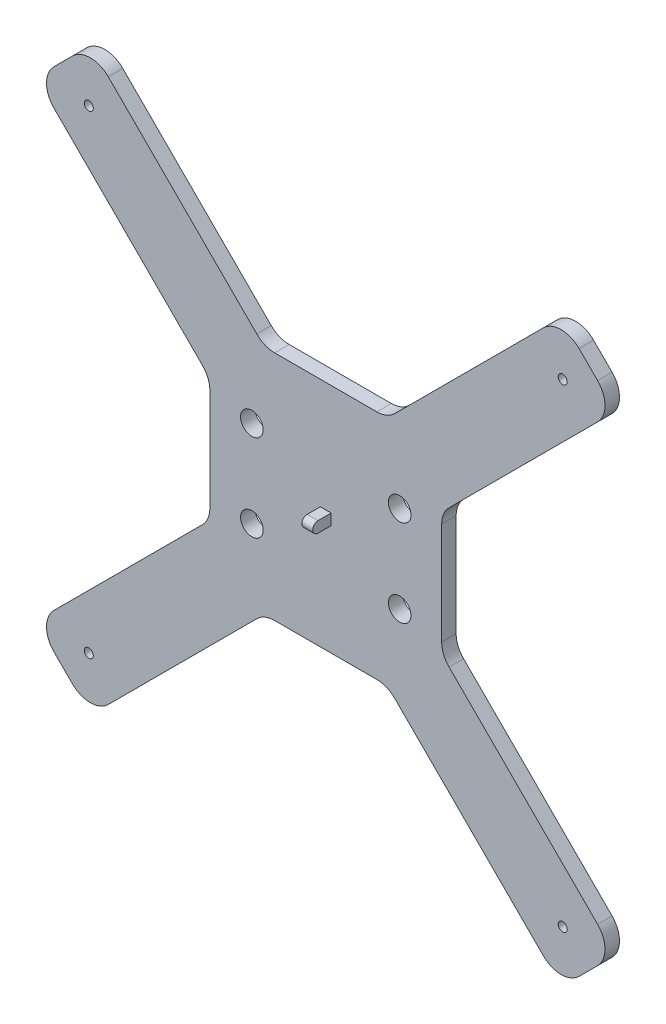
SolidWorks part; units mm, degrees
ref_plane "Front Plane" through (0, 0, 0) normal (0, 0, 1) x (1, 0, 0)
ref_plane "Top Plane" through (0, 0, 0) normal (0, 1, 0) x (1, 0, 0)
ref_plane "Right Plane" through (0, 0, 0) normal (1, 0, 0) x (0, 0, -1)
sketch "Sketch1" plane through (0, 0, 0) normal (0, 0, 1) x (1, 0, 0)
  line L0 (0, 184.15) -> (60.96, 123.19)
  line L5 (19.05, 203.2) -> (80.01, 142.24)
  line L6 (0, 19.05) -> (60.96, 80.01)
  line L7 (19.05, 0) -> (80.01, 60.96)
  line L8 (0, 184.15) -> (19.05, 203.2)
  line L9 (184.15, 203.2) -> (203.2, 184.15)
  line L10 (203.2, 19.05) -> (184.15, 0)
  line L11 (0, 19.05) -> (19.05, 0)
  line L12 (80.01, 142.24) -> (123.19, 142.24)
  line L13 (80.01, 60.96) -> (123.19, 60.96)
  line L14 (60.96, 123.19) -> (60.96, 80.01)
  line L15 (142.24, 123.19) -> (142.24, 80.01)
  line L17 (123.19, 60.96) -> (184.15, 0)
  line L18 (142.24, 80.01) -> (203.2, 19.05)
  line L19 (123.19, 142.24) -> (184.15, 203.2)
  line L20 (142.24, 123.19) -> (203.2, 184.15)
extrude "Boss-Extrude1" add sketch "Sketch1" along normal blind 5.08
fillet "Fillet1" radius 8.89 16 edges at (60.96, 80.01, 2.54) (60.96, 123.19, 2.54) (0, 184.15, 2.54) (19.05, 203.2, 2.54) (80.01, 142.24, 2.54) (123.19, 142.24, 2.54) (184.15, 203.2, 2.54) (203.2, 184.15, 2.54) (142.24, 123.19, 2.54) (142.24, 80.01, 2.54) (203.2, 19.05, 2.54) (184.15, 0, 2.54) (123.19, 60.96, 2.54) (80.01, 60.96, 2.54) (0, 19.05, 2.54) (19.05, 0, 2.54)
sketch "Sketch2" plane through (0, 0, 5.08) normal (0, 0, 1) x (1, 0, 0)
  line L0 (83.6924, 60.96) -> (119.5076, 60.96) construction
  line L1 (119.5076, 142.24) -> (83.6924, 142.24) construction
  line L2 (142.24, 83.6924) -> (142.24, 119.5076) construction
  line L3 (60.96, 119.5076) -> (60.96, 83.6924) construction
  circle A0 centre (127.508, 86.36) radius 3.9687
  circle A1 centre (127.508, 116.84) radius 3.9687
  circle A2 centre (75.692, 86.36) radius 3.9687
  circle A3 centre (75.692, 116.84) radius 3.9687
  dimension "D1" = 7.9375
  dimension "D2" = 7.9375
  dimension "D7" = 7.9375
  dimension "D8" = 7.9375
  dimension "D3" = 25.4
  dimension "D4" = 25.4
  dimension "D5" = 14.732
  dimension "D6" = 14.732
  dimension "D9" = 14.732
  dimension "D10" = 14.732
extrude "Cut-Extrude1" cut sketch "Sketch2" against normal through all
sketch "Sketch3" plane through (0, 0, 5.08) normal (0, 0, 1) x (1, 0, 0)
  line L0 (196.9138, 190.4362) -> (190.4362, 196.9138) construction
  line L1 (177.8638, 196.9138) -> (125.7938, 144.8438) construction
  line L4 (12.7638, 196.9138) -> (6.2862, 190.4362) construction
  line L5 (77.4062, 144.8438) -> (25.3362, 196.9138) construction
  line L6 (6.2862, 12.7638) -> (12.7638, 6.2862) construction
  line L7 (25.3362, 6.2862) -> (77.4062, 58.3562) construction
  line L8 (190.4362, 6.2862) -> (196.9138, 12.7638) construction
  line L9 (125.7938, 58.3562) -> (177.8638, 6.2862) construction
  circle A0 centre (184.6888, 184.7007) radius 1.5875
  circle A1 centre (18.5112, 184.7007) radius 1.5875
  circle A2 centre (18.5112, 18.4993) radius 1.5875
  circle A3 centre (184.6888, 18.4993) radius 1.5875
  dimension "D3" = 3.175
  dimension "D6" = 3.175
  dimension "D7" = 3.175
  dimension "D10" = 3.175
  dimension "D1" = 12.7
  dimension "D2" = 13.462
  dimension "D4" = 12.7
  dimension "D5" = 13.462
  dimension "D8" = 12.7
  dimension "D9" = 13.462
  dimension "D11" = 12.7
  dimension "D12" = 13.462
extrude "Cut-Extrude2" cut sketch "Sketch3" against normal through all
ref_plane "Plane1" through (101.6, 0, 0) normal (1, 0, 0) x (0, 0, -1)
sketch "Sketch5" plane through (101.6, 0, 0) normal (1, 0, 0) x (0, 0, -1)
  line L0 (-5.08, 99.695) -> (-5.08, 103.505)
  line L1 (-5.08, 83.6924) -> (-5.08, 119.5076) construction
  line L2 (-5.08, 103.505) -> (-9.652, 103.505)
  line L3 (-9.652, 99.695) -> (-5.08, 99.695)
  arc A0 (-9.652, 103.505) -> (-9.652, 99.695) centre (-9.652, 101.6) ccw
  point P5 (-5.08, 101.6)
  dimension "D1" = 3.81
  dimension "D2" = 4.572
extrude "Boss-Extrude3" add sketch "Sketch5" along normal mid plane 3.81
